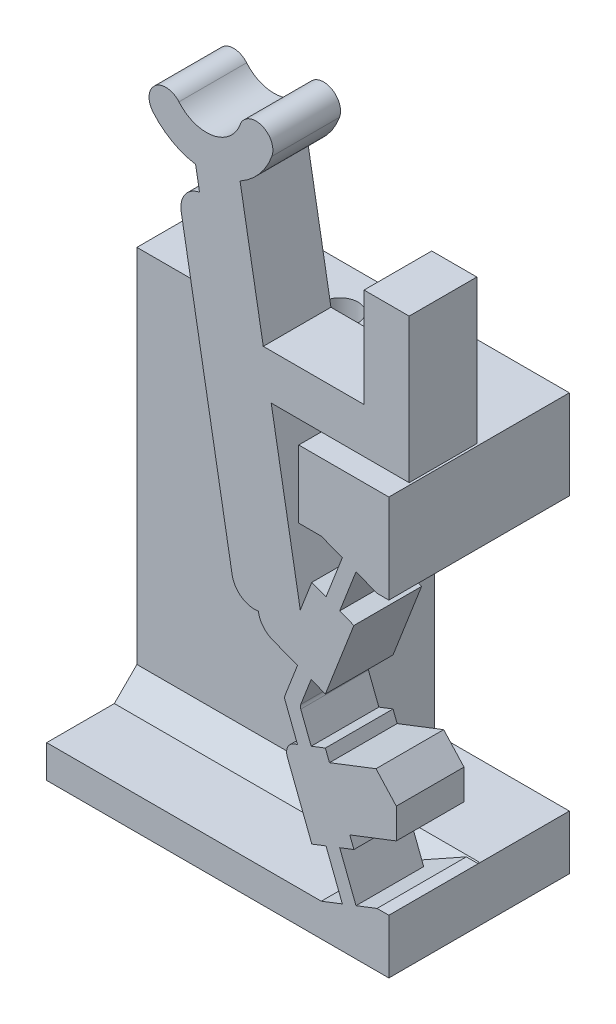
SolidWorks part; units mm, degrees
material "Nylon 6/12"
ref_plane "Front Plane" through (0, 0, 0) normal (0, 0, 1) x (1, 0, 0)
ref_plane "Top Plane" through (0, 0, 0) normal (0, 1, 0) x (1, 0, 0)
ref_plane "Right Plane" through (0, 0, 0) normal (1, 0, 0) x (0, 0, -1)
sketch "Sketch-SkeletonConfigUp" plane through (0, 0, 0) normal (0, 0, 1) x (1, 0, 0)
  line L0 (0, 0) -> (0, -50000) construction
  line L1 (-1.4217, 8.457) -> (-1.4217, 0) construction
  line L3 (0.7468, 14.0514) -> (-1.4217, 8.457) construction
  line L4 (-1.4217, 8.457) -> (0.7468, 2.8626) construction
  line L5 (0.7468, 14.0514) -> (2.1074, 19.3343) construction
  line L6 (-1.4217, 8.457) -> (-5.2203, 30) construction
  line L9 (0.7468, 14.0514) -> (0.7468, 2.8626) construction
  line L10 (0.7468, 2.8626) -> (0.7468, 0) construction
  line L11 (0, 0) -> (0.7468, 0) construction
  line L12 (0.7468, 0) -> (0, 0) construction
  dimension "D7" = 5.4552
  dimension "D10" = 6.745
  dimension "D3" = 2.1685
  dimension "D9" = 10
  dimension "D13" = 11.1888
  dimension "D14" = 30
  dimension "D5" = 10
  dimension "D2" = 21.8753
  dimension "D4" = 6
sketch "Sketch-SkeletonConfigDown" plane through (0, 0, 0) normal (0, 0, 1) x (1, 0, 0)
  line L0 (0, 0) -> (0, -50000) construction
  line L1 (0.7468, 14.0514) -> (0.7468, 2.8626) construction
  line L2 (5.9945, 14.5439) -> (0.7468, 14.0514) construction
  line L3 (0.7468, 14.0514) -> (2.9153, 8.457) construction
  line L4 (2.9153, 8.457) -> (0.7468, 2.8626) construction
  line L5 (0.7468, 14.0514) -> (-1.8086, 18.8711) construction
  line L6 (2.9153, 8.457) -> (-14.411, 21.8109) construction
  line L7 (0.7468, 2.8626) -> (5.9945, 14.5439) construction
  line L8 (-387.6937, -861.8102) -> (5.9945, 14.5439) construction
  line L10 (-1.4217, 8.457) -> (0.7468, 2.8626) construction
  line L11 (0.7468, 14.0514) -> (-1.4217, 8.457) construction
  line L12 (-1.4217, 8.457) -> (-5.2203, 30) construction
  line L13 (0.7468, 14.0514) -> (2.1074, 19.3343) construction
  dimension "D10" = 6.745
  dimension "D4" = 5.2707
  dimension "D5" = 119.553
  dimension "D2" = 52.378
  dimension "D3" = 31.19
ref_plane "Plane-Cam Base" through (3.8672, 0, 0) normal (1, 0, 0) x (0, 0, -1)
ref_plane "Plane-Down-to-Up Derailleur Clearance" through (1.3672, 0, 0) normal (1, 0, 0) x (0, 0, -1)
ref_plane "Plane-Cam Cavity Roof" through (-0.1328, 0, 0) normal (1, 0, 0) x (0, 0, -1)
sketch "Sketch-SwitchBossUp" plane through (0, 0, 0) normal (0, 0, 1) x (1, 0, 0)
  line L8 (-5.6979, 26.9497) -> (-5.5242, 25.9649)
  line L9 (-1.4217, 8.457) -> (-5.2203, 30) construction
  line L15 (-1.1826, 6.941) -> (-0.5766, 7.1759) construction
  line L16 (-1.4217, 8.457) -> (0.7468, 2.8626) construction
  line L19 (0.0824, 13.2365) -> (0.6884, 13.0016) construction
  line L22 (0.8052, 15.1013) -> (1.4113, 14.8664) construction
  line L23 (-1.1826, 9.9731) -> (-1.812, 10.2171)
  line L32 (1.0498, 2.9801) -> (0.4438, 2.7452) construction
  line L40 (-1.7703, 8.457) -> (-1.0732, 8.457) construction
  line L66 (-5.2203, 27.8193) -> (-5.2203, 50027.8193) construction
  line L74 (-4.078, 12.0039) -> (-6.3354, 24.8064)
  line L81 (2.3437, 2.4091) -> (2.8672, 2.4091)
  line L82 (-5.6111, 26.4573) -> (-3.6415, 26.8046) construction
  line L88 (-0.1116, 18.4627) -> (2.8672, 18.4627)
  line L92 (0.6853, 5.7881) -> (-1.1795, 5.0653) construction
  line L95 (-2.3469, 19.4627) -> (3.7672, 19.4627)
  line L96 (2.8672, 14.505) -> (2.8672, 18.4627)
  line L97 (3.7672, 19.4627) -> (3.7672, 25.8576)
  line L101 (-0.8796, 7.0584) -> (-1.4217, 8.457) construction
  line L103 (-5.2203, 30) -> (-3.0238, 29.2005) construction
  line L107 (-1.1826, 9.9731) -> (-0.5766, 9.7382) construction
  line L109 (-5.2203, 30) -> (-7.011, 28.4975) construction
  line L114 (0.0528, 7.4199) -> (-0.5766, 7.1759)
  line L117 (2.8672, 0) -> (-0.1272, 0)
  line L121 (0.7468, 0) -> (0, 0) construction
  line L122 (0.8052, 1.8128) -> (-0.1272, 1.4513)
  line L123 (1.4113, 2.0477) -> (2.3437, 2.4091)
  line L125 (2.8672, 2.4091) -> (2.8672, 0)
  line L127 (-0.5766, 9.7382) -> (0.0528, 9.4942)
  line L133 (0.4438, 14.1689) -> (1.0498, 13.934) construction
  line L134 (0.0528, 9.4942) -> (1.3178, 12.7576)
  line L135 (0.6884, 13.0016) -> (1.3178, 12.7576)
  line L142 (-0.1272, 1.4513) -> (-0.1272, 0)
  line L151 (0.0824, 13.2365) -> (-0.547, 13.4805)
  line L152 (0.8052, 15.1013) -> (0.0824, 13.2365)
  line L153 (1.4113, 14.8664) -> (0.6884, 13.0016)
  line L169 (0.0824, 3.6776) -> (0.8052, 1.8128)
  line L170 (1.4113, 2.0477) -> (0.6884, 3.9125)
  line L177 (0.6884, 3.9125) -> (0.0824, 3.6776) construction
  line L184 (-0.547, 13.4805) -> (-1.0591, 12.1594)
  line L191 (-1.1826, 6.941) -> (-1.812, 6.697)
  line L197 (3.7672, 25.8576) -> (1.7672, 25.8576)
  line L205 (1.7672, 25.8576) -> (1.7672, 21.4627)
  line L207 (12.0045, 16.6962) -> (12.0045, 16.6883) construction
  line L218 (0.6884, 3.9125) -> (1.3178, 4.1564)
  line L225 (-1.0591, 12.1594) -> (-2.3469, 19.4627)
  line L235 (-5.5242, 25.9649) -> (-2.8161, 10.6063) construction
  line L236 (-1.812, 6.697) -> (-0.547, 3.4336)
  line L237 (-2.8161, 10.6063) -> (-2.9195, 11.1927)
  line L241 (-1.4217, 8.457) -> (-0.8796, 9.8556) construction
  line L242 (1.7672, 21.4627) -> (-2.6996, 21.4627)
  line L243 (-0.5766, 7.1759) -> (-1.0381, 8.3667)
  line L244 (-1.0381, 8.5474) -> (-0.5766, 9.7382)
  line L245 (-1.1826, 6.941) -> (-1.7353, 8.3667)
  line L246 (-1.7353, 8.5474) -> (-1.1826, 9.9731)
  line L247 (0.0528, 7.4199) -> (0.2353, 6.9492)
  line L248 (0.8052, 1.8128) -> (1.4113, 2.0477) construction
  line L249 (0.0824, 3.6776) -> (-0.547, 3.4336)
  line L250 (-1.812, 10.2171) -> (-0.547, 13.4805) construction
  line L251 (0.7468, 14.0514) -> (-1.4217, 8.457) construction
  line L252 (-1.2699, 11.6157) -> (0.5949, 10.8928) construction
  line L253 (-2.3469, 19.4627) -> (-2.6996, 21.4627) construction
  line L254 (-1.812, 10.2171) -> (-2.8161, 10.6063)
  line L255 (0.8052, 15.1013) -> (-0.1272, 15.4627)
  line L256 (1.4113, 14.8664) -> (2.3437, 14.505)
  line L257 (2.3437, 14.505) -> (2.8672, 14.505)
  line L258 (-2.6996, 21.4627) -> (-3.7283, 27.297)
  line L259 (3.8672, -55) -> (3.8672, 55) construction
  line L260 (0.2353, 6.9492) -> (2.2973, 7.7484)
  line L261 (3.1975, 6.7619) -> (3.1975, 5.4265)
  line L262 (3.1975, 5.4265) -> (1.1353, 4.6271)
  line L263 (0.6853, 5.7881) -> (3.1975, 6.7619) construction
  line L264 (1.1353, 4.6271) -> (0.6853, 5.7881) construction
  line L265 (1.1353, 4.6271) -> (1.3178, 4.1564)
  line L266 (0.6853, 5.7881) -> (0.2353, 6.9492) construction
  line L267 (0.2353, 6.9492) -> (0.6853, 5.7881) construction
  line L268 (0.6853, 5.7881) -> (1.1353, 4.6271) construction
  line L269 (0.2353, 6.9492) -> (0.6853, 5.7881) construction
  line L270 (0.6853, 5.7881) -> (1.1353, 4.6271) construction
  line L271 (3.1975, 6.7619) -> (2.2973, 7.7484)
  line L272 (1.8311, 5.6598) -> (3.8672, 4.8706) construction
  line L273 (2.9153, 8.457) -> (0.7468, 2.8626) construction
  line L274 (-0.2471, 5.4267) -> (2.2973, 7.7484) construction
  line L275 (-0.2471, 5.4267) -> (3.8672, 5.4267) construction
  line L276 (-0.1272, 15.4627) -> (-1.1272, 15.4627)
  line L277 (-1.1272, 15.4627) -> (-1.1272, 18.4627)
  line L278 (-1.1272, 18.4627) -> (-0.1116, 18.4627)
  arc A0 (-3.7283, 27.297) -> (-2.319, 28.944) centre (-5.2203, 30) ccw
  arc A1 (-5.6979, 26.9497) -> (-7.5855, 28.0154) centre (-5.2203, 30) cw
  arc A2 (-7.5855, 28.0154) -> (-6.4364, 28.9796) centre (-7.011, 28.4975) cw
  arc A3 (-2.319, 28.944) -> (-3.7286, 29.457) centre (-3.0238, 29.2005) ccw
  arc A4 (-6.4364, 28.9796) -> (-3.7286, 29.457) centre (-5.2203, 30) ccw
  arc A19 (-6.3354, 24.8064) -> (-5.5242, 25.9649) centre (-5.3506, 24.98) cw
  circle A28 centre (-5.2203, 30) radius 2.3375 construction
  arc A30 (-4.078, 12.0039) -> (-2.9195, 11.1927) centre (-3.0932, 12.1775) ccw
  arc A31 (-1.0381, 8.3667) -> (-1.0381, 8.5474) centre (-0.805, 8.457) cw
  arc A32 (-1.7353, 8.3667) -> (-1.7353, 8.5474) centre (-1.5022, 8.457) cw
  point P5 (-4.6263, 26.6309)
  point P6 (-0.2471, 5.4267)
  point P45 (-0.3375, 11.2542)
  point P66 (4.5811, 6.2164)
  point P165 (0.7468, 14.0514)
  dimension "D23" = 1.5875
  dimension "D24" = 0.75
  dimension "D21" = 0.25
  dimension "D8" = 0.65
  dimension "D27" = 0.65
  dimension "D26" = 2
  dimension "D3" = 1.5
  dimension "D5" = 1.5
  dimension "D16" = 2
  dimension "D28" = 2
  dimension "D29" = 2
  dimension "D30" = 1
  dimension "D31" = 15
  dimension "D4" = 1.4169
  dimension "D6" = 0.65
  dimension "D7" = 2
  dimension "D11" = 1
  dimension "D10" = 1
  dimension "D9" = 0
  dimension "D12" = 60
  dimension "D13" = 60
  dimension "D14" = 2
  dimension "D15" = 1
  dimension "D17" = 2
  dimension "D19" = 0.1
  dimension "D22" = 42.38
  dimension "D18" = 3
  dimension "D25" = 1
  dimension "D32" = 1
  dimension "D20" = 1
extrude "Boss-Switch Body" add sketch "Sketch-SwitchBossUp" along normal blind 3
sketch "Sketch1" plane through (0, 0, 0) normal (0, 0, -1) x (-1, 0, 0)
  line L0 (-2.8672, 2.4091) -> (0.1272, 2.4091)
  line L1 (-2.8672, 0) -> (0.1272, 0)
  line L2 (-2.8672, 0) -> (-2.8672, 2.4091)
  line L4 (0.1272, 0) -> (0.1272, 2.4091)
  line L5 (1.1272, 14.505) -> (-2.8672, 14.505)
  line L10 (-2.8672, 14.505) -> (-2.8672, 18.4627)
  line L12 (-2.8672, 18.4627) -> (1.1272, 18.4627)
  line L14 (1.1272, 18.4627) -> (1.1272, 14.505)
  line L20 (-2.3437, 2.4091) -> (-2.8672, 2.4091) construction
  line L22 (-2.8672, 2.4091) -> (-2.3437, 2.4091) construction
  line L31 (0.1272, 0) -> (-2.8672, 0) construction
  line L32 (0.1272, 1.4513) -> (0.1272, 0) construction
extrude "Boss-Flange Width" add sketch "Sketch1" along normal blind 5
ref_plane "Plane-Sta2Sit Groove" through (-5.2203, 0, 0) normal (1, 0, 0) x (0, 0, -1)
ref_plane "Plane-Cam Outer Surface" through (-17.3003, 0, 0) normal (1, 0, 0) x (0, 0, -1)
ref_plane "Plane-FlangeTop" through (-12.3003, 0, 0) normal (1, 0, 0) x (0, 0, -1)
sketch "Sketch2" plane through (-12.3003, 0, 0) normal (1, 0, 0) x (0, 0, -1)
  line L0 (5, 18.4627) -> (-3, 18.4627) construction
  line L1 (5, 14.505) -> (1, 14.505)
  line L2 (5, 14.505) -> (5, 18.4627)
  line L3 (5, 18.4627) -> (1, 18.4627)
  line L4 (1, 14.505) -> (1, 18.4627)
  line L5 (5, 14.505) -> (-3, 14.505) construction
  line L11 (5, 1.4513) -> (-3, 1.4513)
  line L12 (5, 1.4513) -> (5, 0)
  line L13 (5, 0) -> (-3, 0)
  line L14 (-3, 1.4513) -> (-3, 0)
  line L15 (0, 8.457) -> (0, 30) construction
  line L16 (-3, 1.4513) -> (-3, 0) construction
  line L17 (5, 2.4091) -> (5, 0) construction
  line L19 (-3, 1.4513) -> (0, 1.4513) construction
  dimension "D1" = 1
extrude "Boss-Flange Height" add sketch "Sketch2" along normal up to surface (12.1731 mm away) up to face at (-0.1272, 1.2868, -0.6667)
sketch "Sketch17" plane through (0, 1.4513, 0) normal (0, -1, 0) x (1, 0, 0)
  line L0 (2.8672, -5) -> (-12.3003, -5)
  line L1 (2.8672, -5) -> (-12.3003, -5) construction
  line L2 (-12.3003, -5) -> (-12.3003, -1)
  line L3 (-12.3003, -1) -> (2.8672, -1)
  line L4 (2.8672, -1) -> (2.8672, -5)
  line L5 (-12.3003, -1) -> (-12.3003, -5) construction
  line L7 (-1.1272, -1) -> (-12.3003, -1) construction
extrude "Boss-Flange Support" add sketch "Sketch17" against normal up to surface (13.0536 mm away) up to face at (-1.4588, 14.505, -0.6)
sketch "Sketch27" plane through (0, 0, 0) normal (0, 0, 1) x (1, 0, 0)
  line L1 (-0.1272, 15.4627) -> (2.3437, 14.505)
  line L2 (2.3437, 14.505) -> (-1.1272, 14.505)
  line L3 (-1.1272, 14.505) -> (-1.1272, 15.4627)
  line L4 (-1.1272, 15.4627) -> (-0.1272, 15.4627)
  line L6 (-1.1272, 14.505) -> (2.8672, 14.505) construction
  line L7 (2.3437, 14.505) -> (1.2712, 14.505) construction
  line L8 (2.3437, 2.4091) -> (-0.1272, 2.4091)
  line L9 (-0.1272, 2.4091) -> (-0.1272, 1.4513)
  line L10 (-0.1272, 1.4513) -> (2.3437, 2.4091)
extrude "Cut-Wall Gap" cut sketch "Sketch27" against normal up to surface (1 mm away) up to face at (-2.6719, 9.207, -1)
ref_plane "Plane-Tap Depth" through (0, 13.4627, 0) normal (0, 1, 0) x (1, 0, 0)
sketch "Sketch-HolePositions" plane through (0, 0, 0) normal (0, -1, 0) x (1, 0, 0)
  line L0 (-12.3003, -3) -> (2.8672, -3) construction
  line L1 (2.8672, -5) -> (-12.3003, -5) construction
  line L2 (2.8672, -5) -> (2.8672, 3) construction
  line L4 (-12.3003, -22.2167) -> (-12.3003, 22.2167) construction
  point P6 (-9.3003, -3)
  point P7 (-5.3003, -3)
  dimension "D1" = 3
  dimension "D2" = 4
  dimension "D3" = 2
sketch "Sketch6" plane through (0, 0, 0) normal (0, -1, 0) x (-1, 0, 0)
  point P0 (9.3003, 3)
  point P3 (5.3003, 3)
hole_wizard "Tap Drill for M2x0.4 Tap1" positions "Sketch6" profile "Sketch5" hole size "M2x0.4" standard "ANSI Metric" end condition through all
sketch "Sketch5" plane through (-9.3003, 0, -3) normal (1, 0, 0) x (0, 0, -1)
  line L0 (0, 0) -> (0, 29.9505)
  line L1 (0, 29.9505) -> (0.8, 29.9505)
  line L2 (0.8, 29.9505) -> (0.8, 0)
  line L5 (0.8, 0) -> (0, 0)
  line L11 (0, -6.35) -> (0, 107.95) construction
  dimension "Thru Hole Dia." = 1.6
  dimension "Thru Hole Depth" = 29.9505
sketch "Sketch9" plane through (0, 0, 0) normal (0, -1, 0) x (1, 0, 0)
  point P0 (-9.3003, -3)
  point P3 (-5.3003, -3)
hole_wizard "M2 Clearance Hole2" positions "Sketch9" profile "Sketch8" hole size "M2" standard "ANSI Metric"
sketch "Sketch8" plane through (-9.3003, 0, -3) normal (1, 0, 0) x (0, 0, -1)
  line L0 (0, 0) -> (0, 14.1838)
  line L1 (0, 14.1838) -> (1.2, 13.4627)
  line L2 (1.2, 13.4627) -> (1.2, 0)
  line L5 (1.2, 0) -> (0, 0)
  line L10 (0, 14.1838) -> (-1.2, 13.4627) construction
  line L11 (0, -6.35) -> (0, 107.95) construction
  dimension "Hole Dia." = 2.4
  dimension "Hole Depth" = 13.4627
  dimension "Drill Angle" = 118
sketch "Sketch-Measurements for Derailleur Ramps" [suppressed] plane through (0, 0, 0) normal (0, 0, 1) x (1, 0, 0)
  line L0 (2.8784, 16.9852) -> (4.2265, 19.8331)
  line L1 (3.5524, 18.4092) -> (3.0492, 18.6474)
  line L2 (1.9779, 11.0613) -> (4.4465, 28.5428) construction
  line L3 (3.0492, 18.6474) -> (-4.0642, 13.8428)
  line L4 (7.1843, 11.0614) -> (-9.9544, 15.2993) construction
  line L5 (3.0492, 18.6474) -> (2.1536, 12.3053)
  line L6 (2.1536, 12.3053) -> (-4.0642, 13.8428)
  line L7 (-0.5075, 16.2451) -> (-0.5075, 18.6474)
  line L8 (-0.5075, 18.6474) -> (3.0492, 18.6474)
  line L9 (7.1843, 11.0614) -> (1.9779, 11.0613)
  line L10 (5.8827, 8.6389) -> (3.2795, 8.6389)
  line L12 (7.1843, 11.0614) -> (4.5811, 6.2164) construction
  line L13 (4.5811, 8.6389) -> (4.5811, 8.7912)
  line L14 (4.5811, 6.2164) -> (5.8827, 8.6389)
  line L15 (1.9779, 11.0613) -> (4.5811, 6.2164) construction
  line L16 (3.2795, 8.6389) -> (4.5811, 6.2164)
  line L17 (5.8827, 8.6389) -> (5.8827, 8.7912)
  dimension "D1" = 3.5567
  dimension "D2" = 1.3016
sketch "Sketch12" [suppressed] plane through (0, 23.1883, 0) normal (0, 1, 0) x (1, 0, 0)
  line L0 (10.0045, 0) -> (12.0045, -3)
  line L1 (12.0045, -3) -> (12.0045, 0)
  line L2 (12.0045, 0) -> (10.0045, 0)
extrude "Cut-Up-to-Down Cantilever Slope" [suppressed] cut sketch "Sketch12" against normal up to next
ref_plane "Plane1" [suppressed] through (0, 6.9404, 0) normal (0, 1, 0) x (1, 0, 0)
sketch "Sketch-Derailleur Location" [suppressed] plane through (0, 6.9404, 0) normal (0, 1, 0) x (1, 0, 0)
  line L0 (12.9465, 0) -> (12.9465, -3)
  line L1 (4.2399, -3) -> (3.2603, -3) construction
  line L2 (-119237.4187, 0) -> (9.8143, 0) construction
  point P0 (12.9465, 0)
  point P8 (12.9465, -1.5)
ref_plane "Plane-Cantilever Cut" [suppressed] through (7.0848, 8.5204, -1.9058) normal (-0.6301, -0.7578, 0.1695) x (-0.7765, 0.6151, -0.1368)
sketch "Sketch14" [suppressed] plane through (7.0848, 8.5204, -1.9058) normal (-0.6301, -0.7578, 0.1695) x (-0.7765, 0.6151, -0.1368)
  line L0 (2.3023, -1.6911) -> (-0.3551, -1.6911)
  line L2 (2.3023, -4.3362) -> (2.3023, -1.6911)
  line L3 (-0.3551, -1.6911) -> (-0.3551, -4.4608)
  line L5 (-0.3551, -4.4608) -> (1.0087, -5.0843)
  line L6 (1.0087, -5.0843) -> (2.3023, -4.3362)
extrude "Cut-Down-to-Up Cantilever Slope" [suppressed] cut sketch "Sketch14" against normal up to next
ref_plane "Plane-Symmetry Plane" through (0, 0, 1.5) normal (0, 0, 1) x (1, 0, 0)
sketch "Sketch-Cable Center Point" plane through (0, 0, 1.5) normal (0, 0, 1) x (1, 0, 0)
  line L0 (-5.2203, 30) -> (-5.0825, 29.2183)
  line L1 (-1.4217, 8.457) -> (-5.2203, 30) construction
  point P0 (-5.2203, 30)
  dimension "D1" = 0.7937
sketch "Sketch28" plane through (0, 0, -1) normal (0, 0, 1) x (1, 0, 0)
  line L0 (2.8672, 14.505) -> (2.8672, 2.4091)
  line L1 (2.3437, 2.4091) -> (2.8672, 2.4091) construction
  line L2 (2.8672, 14.505) -> (-3.1003, 14.505)
  line L3 (-3.1003, 14.505) -> (-3.1003, 2.4091)
  line L4 (-3.1003, 2.4091) -> (2.8672, 2.4091)
  line L6 (-6.5003, 13.4627) -> (-4.1003, 13.4627) construction
  line L7 (-6.5003, 13.4627) -> (-4.1003, 13.4627) construction
  dimension "D1" = 1
chamfer "Chamfer-Flange Support" [suppressed] distance 1.5 angle 45
chamfer "Chamfer-Flange Support 3" distance 1 angle 45 1 edges at (-6.2138, 1.4513, -1)
fillet "Fillet1" radius 1 1 edges at (-2.8161, 10.6063, 1.5)
fillet "Fillet2" radius 0.5 1 edges at (-1.812, 6.697, 1.5)
extrude "Cut-Print Support Clearance" cut sketch "Sketch28" against normal through all
equation "\"axle-diameter\"=2"
equation "\"switch-thickness\"=12"
equation "\"base-width\"=4.0"
equation "\"axle-bushing-radius\"=3"
equation "\"clearance\"= 0.25"
equation "\"arm-width\"=1.5"
equation "\"min-diameter\"=70"
equation "\"alpha\"=143.6120"
equation "\"gamma\"=119.5526"
equation "\"delta\"=145.9637"
equation "\"epsilon\"=6.7452"
equation "\"l_AB\"=8.8212"
equation "\"l_AC\"=4.4914"
equation "\"l_BD\"=5.2707"
equation "\"l_CD\"=3.8848"
equation "\"l_CE\"=10.9181"
equation "\"l_DF\"=5.4552"
equation "\"l_OA\"=7.7221"
equation "\"D7@Sketch-SkeletonConfigUp\" = \"l_DF\""
equation "\"D_groove\"=3.175"
equation "\"D5@Sketch-SkeletonConfigDown\" = \"gamma\""
equation "\"D4@Sketch-SkeletonConfigDown\" = \"l_BD\""
equation "\"hinge_length\"=1.5"
equation "\"hinge_depth\"=0.25"
equation "\"D10@Sketch-SkeletonConfigUp\"=\"epsilon\""
equation "\"D10@Sketch-SkeletonConfigDown\"=\"epsilon\""
equation "\"EE_dx\"=8.9056"
equation "\"EE_dy\"=8.1898"
equation "\"r_groove\"=\"D_groove\"/2"
equation "\"t_wall\"=25.4/16"
equation "\"width_lower\"=\"D_groove\"+\"t_wall\""
equation "\"cable_to_bottom\"=30.6257"
equation "\"switch_EE-up_base_dy\"=24"
equation "\"switch_EE-down_base_dy\"=16"
equation "\"D_axle\"=25.4/8"
equation "\"D_up_to_down\"=16"
equation "\"D_down_to_up\"=25"
equation "\"t_cam_base\"=7.5"
equation "\"D23@Sketch-SwitchBossUp\"=\"D_groove\"/2"
equation "\"D1@Sketch-Cable Center Point\"=\"D_groove\"/4"
